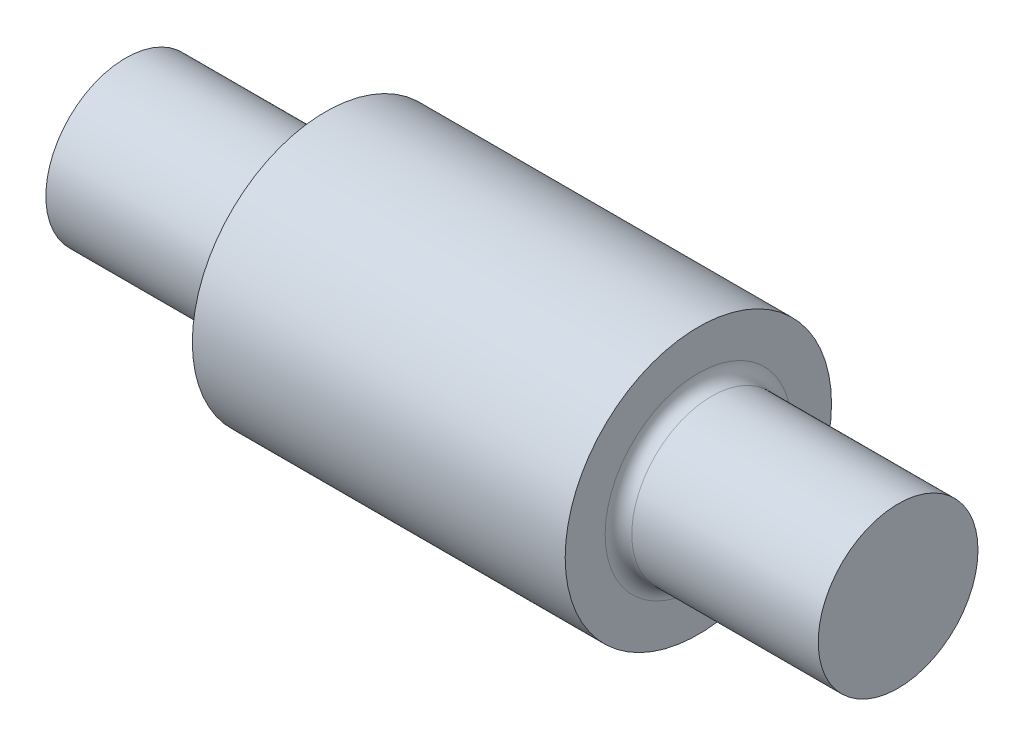
SolidWorks part; units mm, degrees
material "Brass"
ref_plane "Front Plane" through (0, 0, 0) normal (0, 0, 1) x (1, 0, 0)
ref_plane "Top Plane" through (0, 0, 0) normal (0, 1, 0) x (1, 0, 0)
ref_plane "Right Plane" through (0, 0, 0) normal (1, 0, 0) x (0, 0, -1)
sketch "Sketch1" plane through (0, 0, 0) normal (1, 0, 0) x (0, 0, -1)
  circle A0 centre (0, 0) radius 10
  dimension "D1" = 20
extrude "Boss-Extrude1" add sketch "Sketch1" along normal mid plane 28
sketch "草图1" plane through (14, 0, 0) normal (1, 0, 0) x (0, 0, -1)
  circle A0 centre (0, 0) radius 6
extrude "凸台-拉伸1" add sketch "草图1" along normal blind 15
mirror "镜向1" about plane through (0, 0, 0) normal (1, 0, 0) of "凸台-拉伸1"
fillet "圆角1" radius 1 2 edges at (14, 0, -6) (-14, 0, -6)
